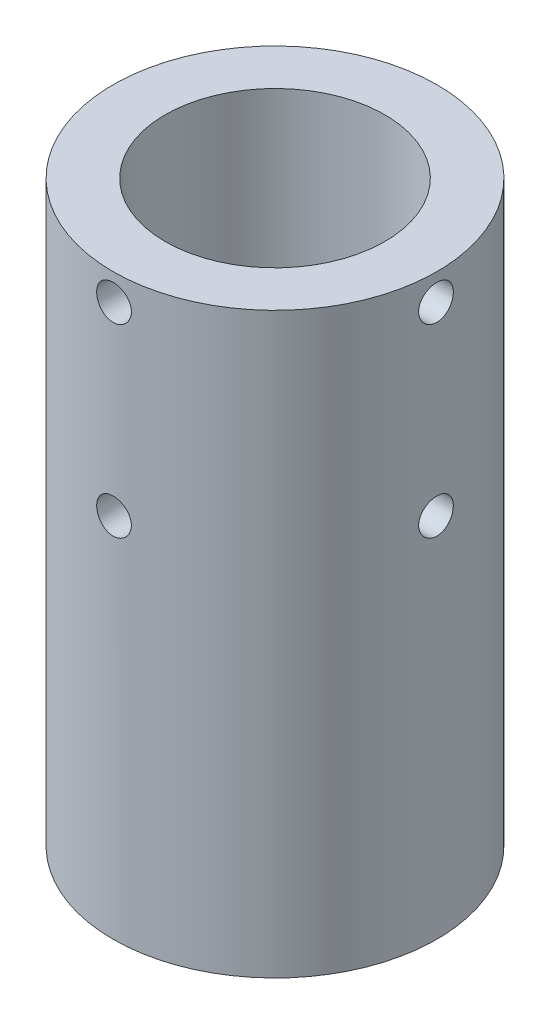
SolidWorks part; units mm, degrees
ref_plane "Front" through (0, 0, 0) normal (0, 0, 1) x (1, 0, 0)
ref_plane "Top" through (0, 0, 0) normal (0, 1, 0) x (1, 0, 0)
ref_plane "Right" through (0, 0, 0) normal (1, 0, 0) x (0, 0, -1)
sketch "Sketch1" plane through (0, 0, 0) normal (0, 1, 0) x (1, 0, 0)
  circle A0 centre (0, 0) radius 14
  dimension "D1" = 28
extrude "Boss-Extrude1" add sketch "Sketch1" along normal blind 50
sketch "Sketch2" plane through (0, 0, 0) normal (0, -1, 0) x (-1, 0, 0)
  line L0 (-2.3979, -5.5) -> (2.3979, -5.5)
  line L1 (-5.9621, 0.6733) -> (-3.5642, 4.8267)
  line L2 (3.5642, 4.8267) -> (5.9621, 0.6733)
  line L3 (0, 0) -> (0, -5.5) construction
  line L4 (0, 0) -> (4.7631, 2.75) construction
  line L5 (0, 0) -> (-4.7631, 2.75) construction
  arc A0 (2.3979, -5.5) -> (5.9621, 0.6733) centre (0, 0) ccw
  arc A1 (-5.9621, 0.6733) -> (-2.3979, -5.5) centre (0, 0) ccw
  arc A2 (3.5642, 4.8267) -> (-3.5642, 4.8267) centre (0, 0) ccw
  dimension "D1" = 12
  dimension "D2" = 5.5
  dimension "D3" = 120
  dimension "D4" = 120
extrude "Cut-Extrude1" cut sketch "Sketch2" against normal blind 33
sketch "Sketch3" plane through (0, 50, 0) normal (0, 1, 0) x (1, 0, 0)
  circle A0 centre (0, 0) radius 9.5
  dimension "D1" = 19
extrude "Cut-Extrude2" cut sketch "Sketch3" against normal blind 24.5
sketch "Sketch4" plane through (0, 50, 0) normal (0, 1, 0) x (1, 0, 0)
  circle A1 centre (0, 0) radius 14 construction
  point P0 (14, 0)
ref_plane "Plane1" through (14, 50, 0) normal (1, 0, 0) x (0, 0, -1)
sketch "Sketch5" plane through (14, 50, 0) normal (1, 0, 0) x (0, 0, -1)
  circle A0 centre (0, -2.3) radius 1.5
  circle A1 centre (0, -18.3) radius 1.5
  dimension "D1" = 3
  dimension "D2" = 2.3
  dimension "D3" = 16
extrude "Cut-Extrude3" cut sketch "Sketch5" against normal up to surface (4.6192 mm away)
pattern_circular "CirPattern1" count 2 over 90 about axis through (0, 33, 0) along (0, -1, 0) of "Cut-Extrude3"
